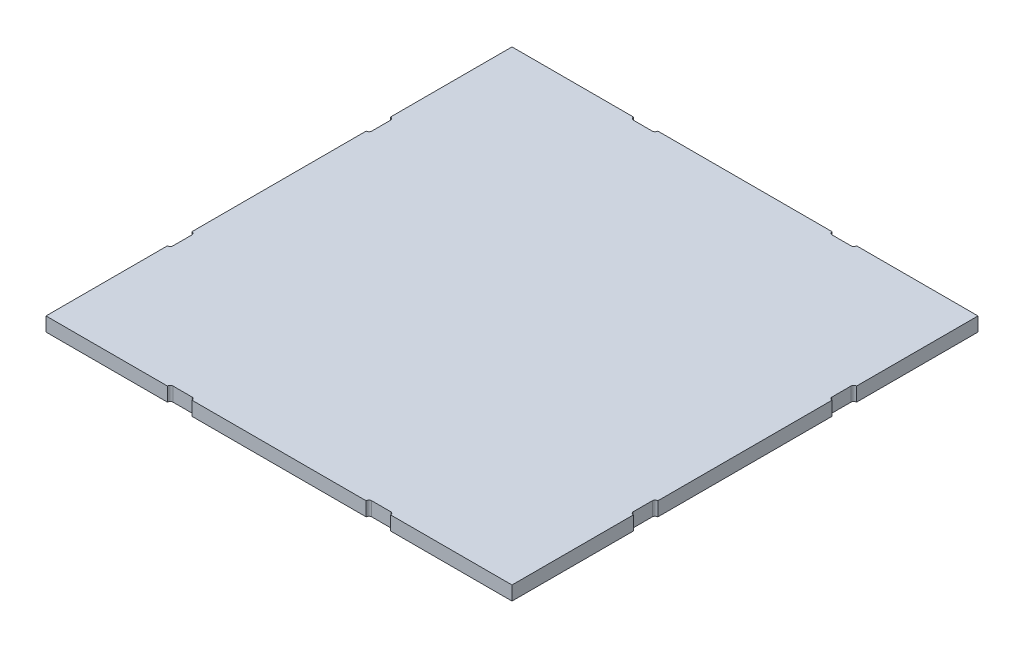
SolidWorks part; units mm, degrees
ref_plane "Front Plane" through (0, 0, 0) normal (0, 0, 1) x (1, 0, 0)
ref_plane "Top Plane" through (0, 0, 0) normal (0, 1, 0) x (1, 0, 0)
ref_plane "Right Plane" through (0, 0, 0) normal (1, 0, 0) x (0, 0, -1)
sketch "Sketch1" plane through (0, 0, 0) normal (0, 1, 0) x (1, 0, 0)
  line L1 (-166.5, 166.5) -> (166.5, 166.5)
  line L2 (-166.5, 166.5) -> (-166.5, -166.5)
  line L3 (-166.5, -166.5) -> (166.5, -166.5)
  line L4 (166.5, 166.5) -> (166.5, -166.5)
  line L5 (-166.5, 166.5) -> (166.5, -166.5) construction
  line L6 (-166.5, -166.5) -> (166.5, 166.5) construction
  point P0 (0, 0)
  dimension "LARGURA" = 333
  dimension "PROFUNDIDADE" = 333
extrude "Boss-Extrude1" add sketch "Sketch1" along normal blind 10
sketch "Sketch2" plane through (0, 10, 0) normal (0, 1, 0) x (1, 0, 0)
  line L0 (-166.5, -166.5) -> (166.5, -166.5) construction
  line L1 (-77.75, -164.5) -> (-64.25, -164.5)
  line L2 (-79.75, -166.5) -> (-79.75, -168.5)
  line L3 (-79.75, -168.5) -> (-62.25, -168.5)
  line L4 (-62.25, -166.5) -> (-62.25, -168.5)
  line L5 (-79.75, -164.5) -> (-62.25, -168.5) construction
  line L6 (-79.75, -168.5) -> (-62.25, -164.5) construction
  line L7 (-166.5, 166.5) -> (-166.5, -166.5) construction
  line L8 (0, -230.3274) -> (0, 199.7202) construction
  line L9 (-190.9314, 0) -> (209.2822, 0) construction
  line L10 (166.5, -166.5) -> (166.5, 166.5) construction
  line L11 (166.5, -62.25) -> (168.5, -62.25)
  line L12 (164.5, -64.25) -> (164.5, -77.75)
  line L13 (166.5, -79.75) -> (168.5, -79.75)
  line L14 (168.5, -62.25) -> (168.5, -79.75)
  line L15 (164.5, -62.25) -> (168.5, -79.75) construction
  line L16 (164.5, -79.75) -> (168.5, -62.25) construction
  line L17 (79.75, -168.5) -> (62.25, -164.5) construction
  line L18 (79.75, -164.5) -> (62.25, -168.5) construction
  line L19 (62.25, -166.5) -> (62.25, -168.5)
  line L20 (79.75, -168.5) -> (62.25, -168.5)
  line L21 (79.75, -166.5) -> (79.75, -168.5)
  line L22 (77.75, -164.5) -> (64.25, -164.5)
  line L23 (164.5, 79.75) -> (168.5, 62.25) construction
  line L24 (164.5, 62.25) -> (168.5, 79.75) construction
  line L25 (168.5, 62.25) -> (168.5, 79.75)
  line L26 (166.5, 79.75) -> (168.5, 79.75)
  line L27 (164.5, 64.25) -> (164.5, 77.75)
  line L28 (166.5, 62.25) -> (168.5, 62.25)
  line L29 (-164.5, 62.25) -> (-168.5, 79.75) construction
  line L30 (-164.5, 79.75) -> (-168.5, 62.25) construction
  line L31 (-166.5, 62.25) -> (-168.5, 62.25)
  line L32 (-164.5, 64.25) -> (-164.5, 77.75)
  line L33 (-166.5, 79.75) -> (-168.5, 79.75)
  line L34 (-168.5, 62.25) -> (-168.5, 79.75)
  line L35 (-164.5, -79.75) -> (-168.5, -62.25) construction
  line L36 (-164.5, -62.25) -> (-168.5, -79.75) construction
  line L37 (-168.5, -62.25) -> (-168.5, -79.75)
  line L38 (-166.5, -79.75) -> (-168.5, -79.75)
  line L39 (-164.5, -64.25) -> (-164.5, -77.75)
  line L40 (-166.5, -62.25) -> (-168.5, -62.25)
  line L41 (79.75, 164.5) -> (62.25, 168.5) construction
  line L42 (79.75, 168.5) -> (62.25, 164.5) construction
  line L43 (77.75, 164.5) -> (64.25, 164.5)
  line L44 (79.75, 166.5) -> (79.75, 168.5)
  line L45 (79.75, 168.5) -> (62.25, 168.5)
  line L46 (62.25, 166.5) -> (62.25, 168.5)
  line L47 (-79.75, 168.5) -> (-62.25, 164.5) construction
  line L48 (-79.75, 164.5) -> (-62.25, 168.5) construction
  line L49 (-62.25, 166.5) -> (-62.25, 168.5)
  line L50 (-79.75, 168.5) -> (-62.25, 168.5)
  line L51 (-79.75, 166.5) -> (-79.75, 168.5)
  line L52 (-77.75, 164.5) -> (-64.25, 164.5)
  arc A0 (-62.25, -166.5) -> (-64.25, -164.5) centre (-64.25, -166.5) ccw
  arc A1 (-77.75, -164.5) -> (-79.75, -166.5) centre (-77.75, -166.5) ccw
  arc A2 (164.5, -64.25) -> (166.5, -62.25) centre (166.5, -64.25) cw
  arc A3 (164.5, -77.75) -> (166.5, -79.75) centre (166.5, -77.75) ccw
  arc A4 (77.75, -164.5) -> (79.75, -166.5) centre (77.75, -166.5) cw
  arc A5 (62.25, -166.5) -> (64.25, -164.5) centre (64.25, -166.5) cw
  arc A6 (164.5, 77.75) -> (166.5, 79.75) centre (166.5, 77.75) cw
  arc A7 (164.5, 64.25) -> (166.5, 62.25) centre (166.5, 64.25) ccw
  arc A8 (-164.5, 64.25) -> (-166.5, 62.25) centre (-166.5, 64.25) cw
  arc A9 (-164.5, 77.75) -> (-166.5, 79.75) centre (-166.5, 77.75) ccw
  arc A10 (-164.5, -77.75) -> (-166.5, -79.75) centre (-166.5, -77.75) cw
  arc A11 (-164.5, -64.25) -> (-166.5, -62.25) centre (-166.5, -64.25) ccw
  arc A12 (62.25, 166.5) -> (64.25, 164.5) centre (64.25, 166.5) ccw
  arc A13 (77.75, 164.5) -> (79.75, 166.5) centre (77.75, 166.5) ccw
  arc A14 (-77.75, 164.5) -> (-79.75, 166.5) centre (-77.75, 166.5) cw
  arc A15 (-62.25, 166.5) -> (-64.25, 164.5) centre (-64.25, 166.5) cw
  point P0 (-71, -166.5)
  point P14 (166.5, -71)
  point P37 (71, -166.5)
  point P48 (166.5, 71)
  point P57 (-71, -166.5)
  point P66 (-166.5, 71)
  point P77 (-166.5, -71)
  point P88 (71, 166.5)
  point P99 (-71, 166.5)
  dimension "D7" = 2
  dimension "D8" = 2
  dimension "D1" = 17.5
  dimension "D2" = 2
  dimension "D3" = 95.5
  dimension "D4" = 2
  dimension "D5" = 17.5
  dimension "D6" = 95.5
extrude "Cut-Extrude1" cut sketch "Sketch2" against normal through all
